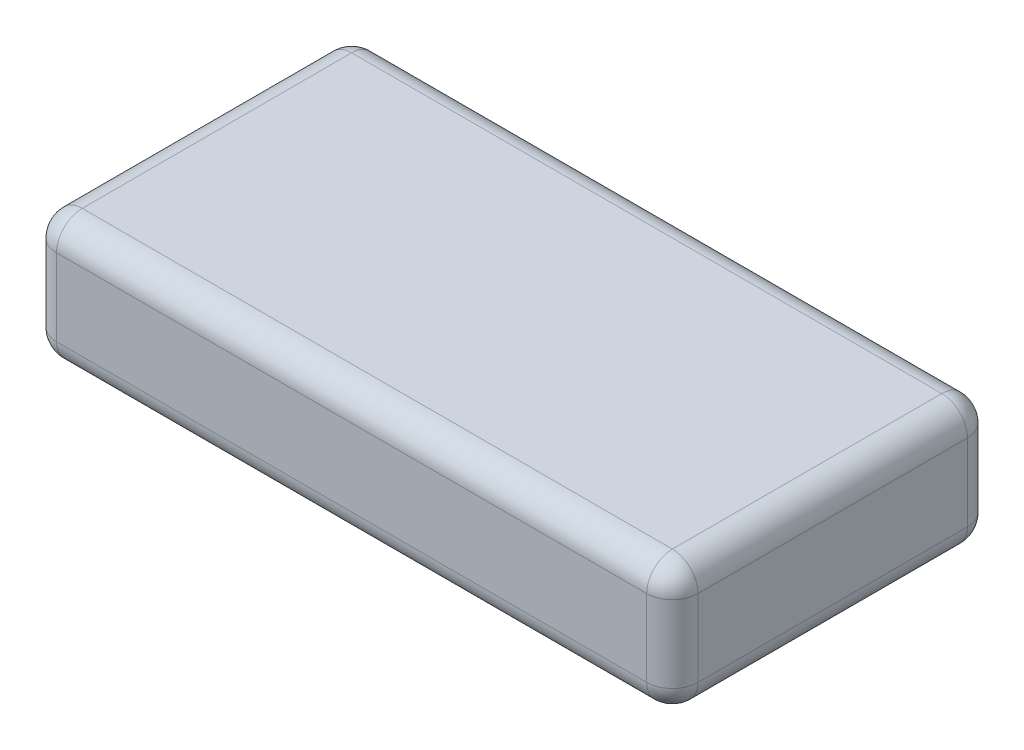
SolidWorks part; units mm, degrees
ref_plane "前视基准面" through (0, 0, 0) normal (0, 0, 1) x (1, 0, 0)
ref_plane "上视基准面" through (0, 0, 0) normal (0, 1, 0) x (1, 0, 0)
ref_plane "右视基准面" through (0, 0, 0) normal (1, 0, 0) x (0, 0, -1)
sketch "草图1" plane through (0, 0, 0) normal (0, 1, 0) x (1, 0, 0)
  line L1 (0, 0) -> (10, 0)
  line L2 (0, 0) -> (0, -5)
  line L3 (0, -5) -> (10, -5)
  line L4 (10, 0) -> (10, -5)
  dimension "D1" = 10
  dimension "D2" = 5
extrude "凸台-拉伸1" add sketch "草图1" along normal blind 2
fillet "圆角1" radius 0.4 12 edges at (0, 1, 0) (0, 2, 2.5) (0, 1, 5) (0, 0, 2.5) (10, 1, 5) (10, 1, 0) (5, 0, 0) (5, 0, 5) (10, 0, 2.5) (10, 2, 2.5) (5, 2, 0) (5, 2, 5)
